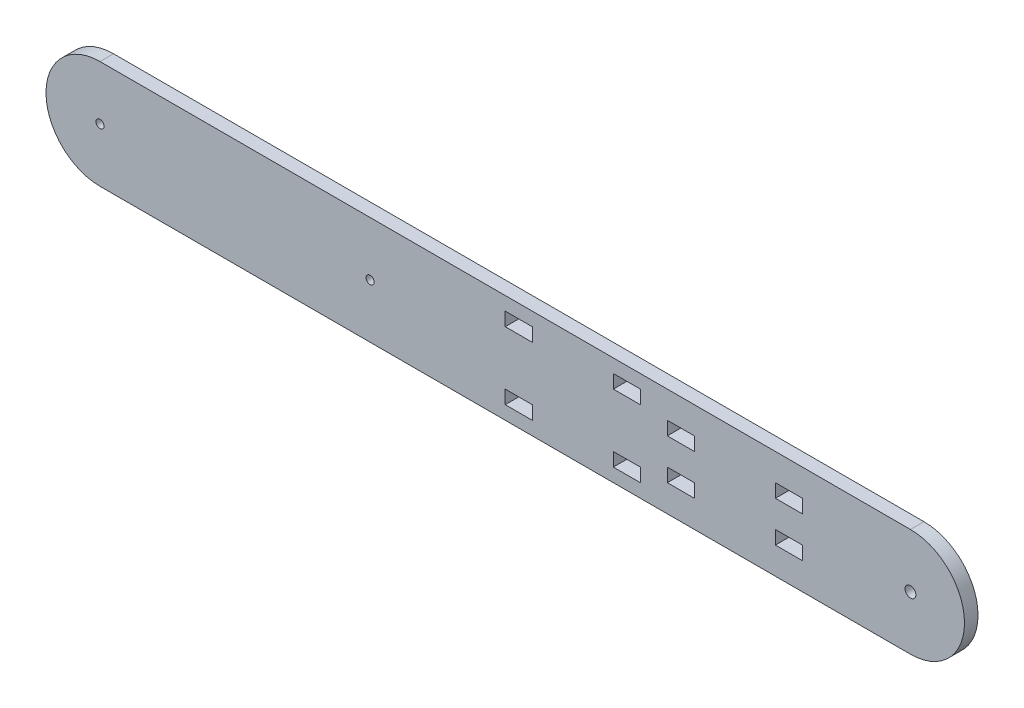
SolidWorks part; units mm, degrees
ref_plane "Front Plane" through (0, 0, 0) normal (0, 0, 1) x (1, 0, 0)
ref_plane "Top Plane" through (0, 0, 0) normal (0, 1, 0) x (1, 0, 0)
ref_plane "Right Plane" through (0, 0, 0) normal (1, 0, 0) x (0, 0, -1)
sketch "Sketch1" plane through (0, 0, 0) normal (0, 0, 1) x (1, 0, 0)
  line L0 (-126.9044, 0) -> (173.0956, 0) construction
  line L1 (-126.9044, 20) -> (173.0956, 20)
  line L2 (-126.9044, -20) -> (173.0956, -20)
  line L3 (173.0956, 15) -> (-126.9044, 15) construction
  line L4 (173.0956, 10) -> (-126.9044, 10) construction
  line L5 (-126.9044, -15) -> (173.0956, -15) construction
  line L6 (173.0956, -10) -> (-126.9044, -10) construction
  line L7 (-126.9044, -5) -> (173.0956, -5) construction
  line L8 (173.0956, 5) -> (-126.9044, 5) construction
  line L9 (23.0956, -20) -> (23.0956, 20) construction
  line L10 (-57.7377, 20) -> (-57.7377, -20) construction
  line L11 (23.0956, 15) -> (33.0956, 15)
  line L12 (23.0956, 15) -> (23.0956, 10)
  line L13 (23.0956, 10) -> (33.0956, 10)
  line L14 (33.0956, 15) -> (33.0956, 10)
  line L15 (63.0956, 15) -> (73.0956, 15)
  line L16 (63.0956, 15) -> (63.0956, 10)
  line L17 (63.0956, 10) -> (73.0956, 10)
  line L18 (73.0956, 15) -> (73.0956, 10)
  line L19 (83.0956, 10) -> (93.0956, 10)
  line L20 (83.0956, 10) -> (83.0956, 5)
  line L21 (83.0956, 5) -> (93.0956, 5)
  line L22 (93.0956, 10) -> (93.0956, 5)
  line L23 (123.0956, 10) -> (133.0956, 10)
  line L24 (123.0956, 10) -> (123.0956, 5)
  line L25 (123.0956, 5) -> (133.0956, 5)
  line L26 (133.0956, 10) -> (133.0956, 5)
  line L27 (33.0956, -15) -> (23.0956, -15)
  line L28 (33.0956, -15) -> (33.0956, -10)
  line L29 (33.0956, -10) -> (23.0956, -10)
  line L30 (23.0956, -15) -> (23.0956, -10)
  line L31 (63.0956, -15) -> (73.0956, -15)
  line L32 (63.0956, -15) -> (63.0956, -10)
  line L33 (63.0956, -10) -> (73.0956, -10)
  line L34 (73.0956, -15) -> (73.0956, -10)
  line L35 (83.0956, -10) -> (93.0956, -10)
  line L36 (83.0956, -10) -> (83.0956, -5)
  line L37 (83.0956, -5) -> (93.0956, -5)
  line L38 (93.0956, -10) -> (93.0956, -5)
  line L39 (123.0956, -5) -> (133.0956, -5)
  line L40 (123.0956, -5) -> (123.0956, -10)
  line L41 (123.0956, -10) -> (133.0956, -10)
  line L42 (133.0956, -5) -> (133.0956, -10)
  arc A0 (-126.9044, 20) -> (-126.9044, -20) centre (-126.9044, 0) ccw
  arc A1 (173.0956, -20) -> (173.0956, 20) centre (173.0956, 0) ccw
  circle A2 centre (-126.9044, 0) radius 1.5
  circle A3 centre (173.0956, 0) radius 2
  circle A5 centre (-26.9044, 0) radius 1.5
  point P3 (23.0956, 0)
  dimension "D3" = 3
  dimension "D4" = 4
  dimension "D22" = 3
  dimension "D23" = 100
  dimension "D1" = 300
  dimension "D2" = 40
  dimension "D5" = 5
  dimension "D6" = 5
  dimension "D7" = 5
  dimension "D8" = 10
  dimension "D9" = 5
  dimension "D10" = 5
  dimension "D11" = 150
  dimension "D12" = 10
  dimension "D13" = 10
  dimension "D14" = 30
  dimension "D15" = 10
  dimension "D16" = 10
  dimension "D17" = 30
  dimension "D18" = 10
  dimension "D19" = 10
  dimension "D20" = 10
  dimension "D21" = 30
extrude "Boss-Extrude2" add sketch "Sketch1" along normal blind 5
